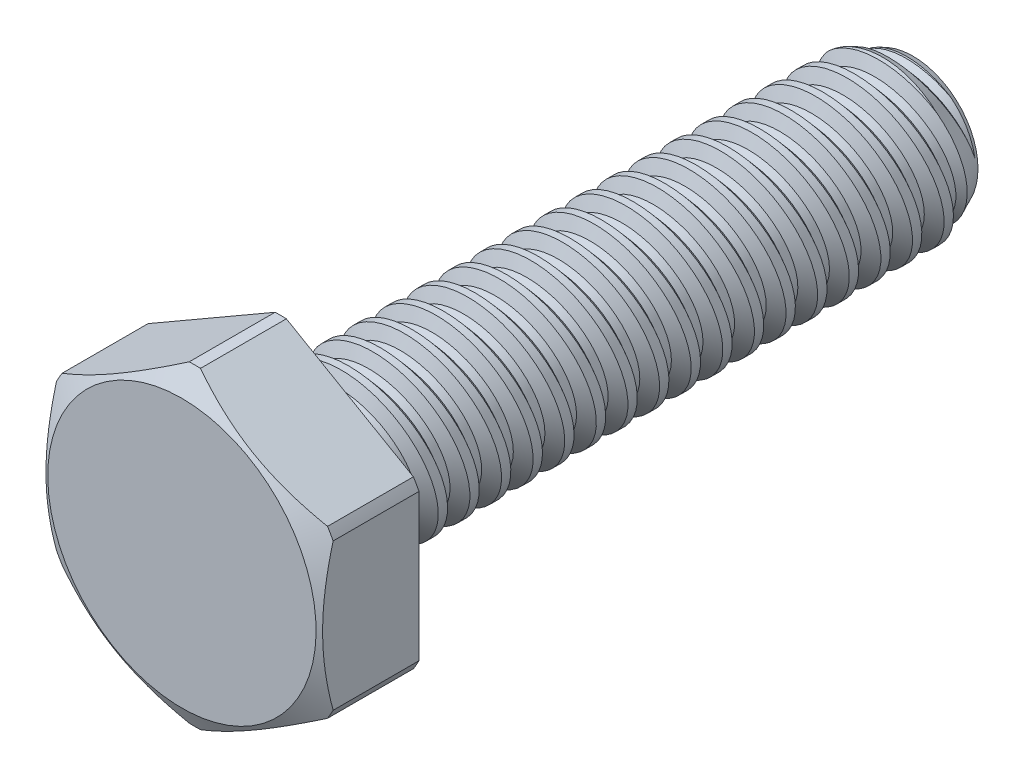
SolidWorks part; units mm, degrees
material "Plain Carbon Steel"
ref_plane "Front" through (0, 0, 0) normal (0, 0, 1) x (1, 0, 0)
ref_plane "Top" through (0, 0, 0) normal (0, 1, 0) x (1, 0, 0)
ref_plane "Right" through (0, 0, 0) normal (1, 0, 0) x (0, 0, -1)
sketch "Sketch1" plane through (0, 0, 0) normal (1, 0, 0) x (0, 0, -1)
  line L0 (-12.7, 0) -> (-16.6687, 0) construction
  line L1 (-12.7, 0) -> (-12.7, 5.5563) construction
  line L2 (-12.7, 0) -> (-16.6687, 0) construction
  line L3 (-12.7, -3.175) -> (12.7, -3.175) construction
  line L4 (-12.7, 0) -> (12.7, 0)
  line L5 (-12.7, 0) -> (-12.7, 3.175)
  line L6 (-12.7, 3.175) -> (12.7, 3.175)
  line L7 (12.7, 0) -> (12.7, 3.175)
  dimension "Screw Dia" = 6.35
  dimension "Screw Length" = 25.4
  dimension "Head Height" = 3.9688
  dimension "Head Width" = 11.1125
revolve "Revolve1" add sketch "Sketch1" angle 360 about L0
sketch "Sketch2" plane through (0, 0, 0) normal (1, 0, 0) x (0, 0, -1)
  line L0 (-12.7, 3.175) -> (-12.7, -3.175) construction
  line L1 (-12.7, -3.175) -> (-11.43, -3.175) construction
  line L2 (-11.43, -3.175) -> (-12.7, 3.175) construction
  line L3 (-12.7, 3.175) -> (-12.5443, 3.2061) construction
  line L4 (-11.4547, 3.4241) -> (-12.5443, 3.2061)
  line L5 (-12.5443, 3.2061) -> (-12.0204, 2.6099)
  line L6 (-12.0204, 2.6099) -> (-11.709, 2.6722)
  line L7 (-11.709, 2.6722) -> (-11.4547, 3.4241)
  line L8 (-11.8647, 2.641) -> (-11.9995, 3.3151) construction
  line L9 (-12.7, 0) -> (-12.7, 3.175) construction
  line L10 (-12.7, 3.175) -> (-11.9715, 3.175) construction
  line L11 (-11.9715, 3.175) -> (-10.7015, -3.175) construction
  line L12 (-10.7015, -3.175) -> (-11.43, -3.175) construction
  line L13 (-12.7, -3.175) -> (12.7, -3.175) construction
  line L14 (-12.7, -0.2727) -> (-9.973, 0.2727) construction
  line L15 (-12.7, 3.175) -> (12.7, 3.175) construction
  point P17 (-11.3365, 0)
  dimension "D1" = 1.27
  dimension "Thread Pitch" = 1.27
  dimension "D3" = 0.3175
  dimension "D4" = 0.1588
  dimension "D5" = 60
revolve "Cut-Revolve1" cut sketch "Sketch2" angle 360 about L14
sketch "Sketch3" plane through (0, 0, 0) normal (1, 0, 0) x (0, 0, -1)
  line L0 (11.4882, 3.175) -> (12.7, 2.6099)
  line L1 (12.7, 2.6099) -> (12.7, 3.175)
  line L2 (12.7, 3.175) -> (11.4882, 3.175)
  line L3 (-12.7, 3.175) -> (12.7, 3.175) construction
  line L4 (12.7, 0) -> (12.7, 3.175) construction
  line L5 (-12.0204, 2.6099) -> (12.7, 2.6099) construction
  line L6 (11.4882, 3.175) -> (11.4882, -3.175) construction
  line L7 (-12.7, -3.175) -> (12.7, -3.175) construction
  line L8 (0, 0) -> (11.4882, 0) construction
  dimension "D1" = 25
  dimension "D2" = 6.35
revolve "Cut-Revolve2" cut sketch "Sketch3" angle 360 about L8
pattern_linear "LPattern1" count 2 spacing 1.27 along (0, 0, 1) count 20 spacing 1.27 along (0, 0, 1)
sketch "Sketch5" plane through (0, 0, 12.7) normal (0, 0, 1) x (1, 0, 0)
  line L1 (0, 6.4158) -> (-5.5562, 3.2079)
  line L2 (-5.5562, 3.2079) -> (-5.5562, -3.2079)
  line L3 (-5.5562, -3.2079) -> (0, -6.4158)
  line L4 (0, -6.4158) -> (5.5562, -3.2079)
  line L5 (5.5562, -3.2079) -> (5.5562, 3.2079)
  line L6 (5.5562, 3.2079) -> (0, 6.4158)
  circle A0 centre (0, 0) radius 5.5563 construction
  dimension "D1" = 11.1125
extrude "Extrude1" add sketch "Sketch5" along normal up to vertex
sketch "Sketch6" plane through (0, 0, 0) normal (1, 0, 0) x (0, 0, -1)
  line L0 (-16.6687, 5.3896) -> (-16.1496, 6.2888)
  line L1 (-16.1496, 6.2888) -> (-12.7, 6.2888)
  line L2 (-12.7, 6.2888) -> (-12.7, 6.7968)
  line L3 (-12.7, 6.7968) -> (-16.6687, 6.7968)
  line L4 (-16.6687, 6.7968) -> (-16.6687, 5.3896)
  line L5 (-16.6687, 3.2079) -> (-16.6687, 6.4158) construction
  line L6 (-16.6687, 6.4158) -> (-12.7, 6.4158) construction
  line L7 (-12.7, 3.2079) -> (-12.7, 6.4158) construction
  line L8 (0, 0) -> (-16.1496, 0) construction
  line L9 (-12.7, 0) -> (-16.6687, 0) construction
  line L10 (-16.1496, 0) -> (-16.1496, 6.2888) construction
  line L11 (-14.6844, 6.7968) -> (-14.6844, 0) construction
  dimension "D1" = 30
  dimension "D2" = 0.127
  dimension "D3" = 0.508
  dimension "D4" = 10.7791
  dimension "D5" = 3.9688
  dimension "D6" = 25.4
revolve "Cut-Revolve3" cut sketch "Sketch6" angle 360 about L8
equation "\"D3@Sketch2\"=\"Thread Pitch@Sketch2\"/4"
equation "\"D4@Sketch2\"=\"Thread Pitch@Sketch2\"/8"
equation "\"D1@Sketch2\"=\"Thread Pitch@Sketch2\""
equation "\"D3@LPattern1\"=\"Thread Pitch@Sketch2\""
equation "\"D4@LPattern1\"=\"Thread Pitch@Sketch2\""
equation "\"D4@Sketch6\"=\"Head Width@Sketch1\"*.97"
equation "\"D2@LPattern1\"=\"Screw Length@Sketch1\"/\"Thread Pitch@Sketch2\""
